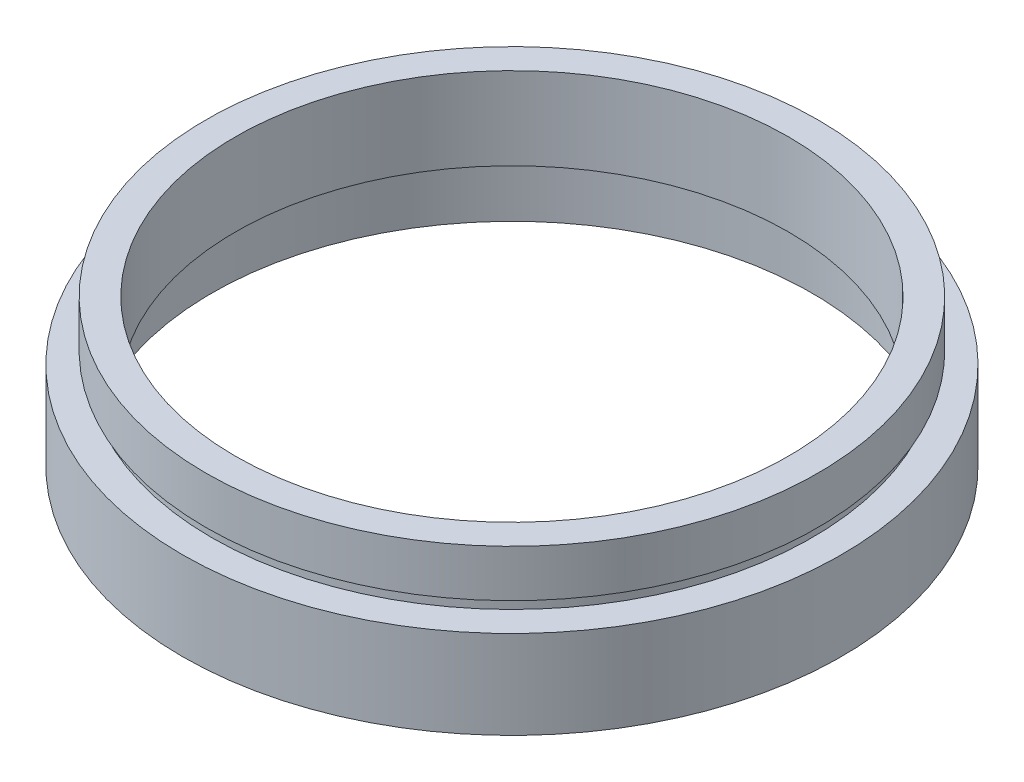
SolidWorks part; units mm, degrees
ref_plane "前视基准面" through (0, 0, 0) normal (0, 0, 1) x (1, 0, 0)
ref_plane "上视基准面" through (0, 0, 0) normal (0, 1, 0) x (1, 0, 0)
ref_plane "右视基准面" through (0, 0, 0) normal (1, 0, 0) x (0, 0, -1)
sketch "草图1" plane through (0, 0, 0) normal (0, 0, 1) x (1, 0, 0)
  line L0 (0, 161.3762) -> (0, 0) construction
  line L1 (141.7365, 0) -> (-131.7984, 0) construction
  line L2 (23.5, 12.5) -> (26, 12.5)
  line L3 (26, 12.5) -> (26, 8.5)
  line L4 (26, 8.5) -> (25.5, 8.5)
  line L5 (25.5, 8.5) -> (25.5, 7.5)
  line L6 (25.5, 7.5) -> (28, 7.5)
  line L7 (28, 7.5) -> (28, 0)
  line L8 (28, 0) -> (25.5, 0)
  line L9 (25.5, 0) -> (25.5, 4.5)
  line L10 (25.5, 4.5) -> (26.1, 4.5)
  line L11 (26.1, 4.5) -> (26.1, 5.5)
  line L12 (26.1, 5.5) -> (23.5, 5.5)
  line L13 (23.5, 5.5) -> (23.5, 12.5)
  dimension "D1" = 23.5
  dimension "D2" = 26
  dimension "D3" = 1
  dimension "D4" = 1
  dimension "D5" = 25.5
  dimension "D6" = 26.1
  dimension "D7" = 25.5
  dimension "D8" = 5
  dimension "D9" = 7
  dimension "D10" = 7.5
  dimension "D11" = 28
revolve "旋转1" add sketch "草图1" angle 360 about L0
cosmetic thread "装饰螺纹线1" parameters "D2"=52
cosmetic thread "装饰螺纹线2" parameters "D2"=48
cosmetic thread "装饰螺纹线3" parameters "D2"=51
